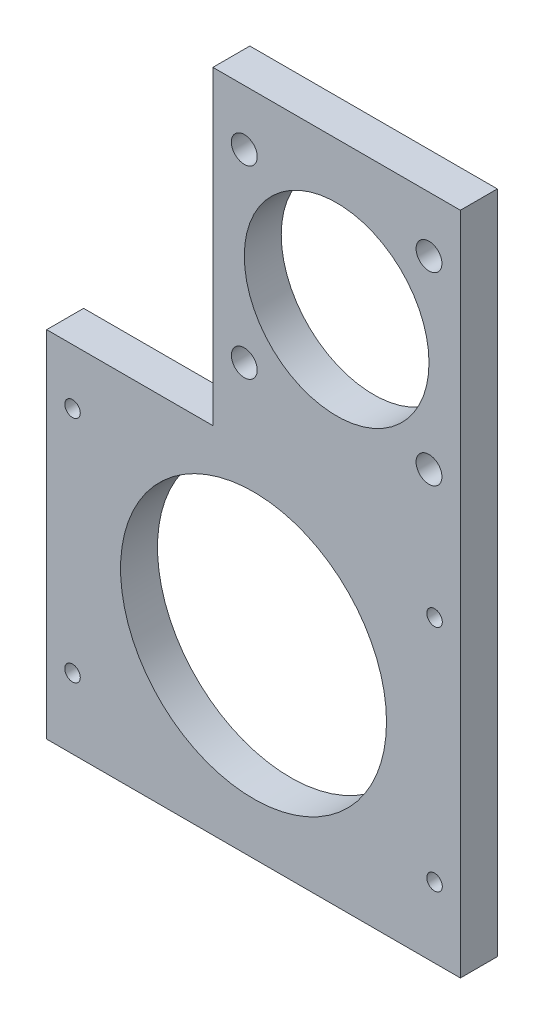
SolidWorks part; units mm, degrees
ref_plane "前视基准面" through (0, 0, 0) normal (0, 0, 1) x (1, 0, 0)
ref_plane "上视基准面" through (0, 0, 0) normal (0, 1, 0) x (1, 0, 0)
ref_plane "右视基准面" through (0, 0, 0) normal (1, 0, 0) x (0, 0, -1)
sketch "草图1" plane through (0, 0, 0) normal (0, 0, 1) x (1, 0, 0)
  line L0 (0, 0) -> (0, 23.9514) construction
  line L1 (-11, 90) -> (56, 90)
  line L2 (-56, 6) -> (-56, -90)
  line L3 (-56, -90) -> (56, -90)
  line L4 (56, 90) -> (56, -90)
  line L5 (-20.7857, 33.4056) -> (56, -90) construction
  line L6 (-56, -90) -> (56, 90) construction
  line L7 (-133.554, 0) -> (85.9905, 0) construction
  line L8 (-11, 90) -> (-11, 6)
  line L9 (-11, 6) -> (-56, 6)
  circle A0 centre (0, -40) radius 36
  circle A1 centre (22.5, 50) radius 25
  point P0 (0, 0)
  dimension "D3" = 96
  dimension "D9" = 50
  dimension "D10" = 72
  dimension "D1" = 112
  dimension "D2" = 180
  dimension "D4" = 67
  dimension "D5" = 40
  dimension "D6" = 50
  dimension "D7" = 56
  dimension "D8" = 33.5
extrude "凸台-拉伸1" add sketch "草图1" along normal blind 10
sketch "草图2" plane through (0, 0, 0) normal (0, 0, -1) x (-1, 0, 0)
  line L1 (-49, -9) -> (49, -9)
  line L2 (-49, -9) -> (-49, -71)
  line L3 (-49, -71) -> (49, -71)
  line L4 (49, -9) -> (49, -71)
  line L5 (-49, -9) -> (49, -71) construction
  line L6 (-49, -71) -> (49, -9) construction
  point P0 (0, -40)
  dimension "D1" = 98
  dimension "D2" = 62
sketch "草图3" plane through (0, 0, 0) normal (0, 0, -1) x (-1, 0, 0)
  line L1 (-47.5, 75) -> (2.5, 75)
  line L2 (-47.5, 75) -> (-47.5, 25)
  line L3 (-47.5, 25) -> (2.5, 25)
  line L4 (2.5, 75) -> (2.5, 25)
  line L5 (-47.5, 75) -> (2.5, 25) construction
  line L6 (-47.5, 25) -> (2.5, 75) construction
  point P0 (-22.5, 50)
  dimension "D1" = 50
hole_wizard "M5 螺纹孔1" positions "3D草图1" profile "草图4" tap size "M5" standard "GB"
sketch3d "3D草图1"
  point P0 (49, -9, 0)
  point P3 (-49, -9, 0)
  point P6 (-49, -71, 0)
  point P9 (49, -71, 0)
sketch "草图4" plane through (49, -9, 0) normal (1, 0, 0) x (0, 1, 0)
  line L0 (0, 0) -> (0, 13.6618)
  line L1 (0, 13.6618) -> (2.1, 12.4)
  line L2 (2.1, 12.4) -> (2.1, 0)
  line L5 (2.1, 0) -> (0, 0)
  line L10 (0, 13.6618) -> (-2.1, 12.4) construction
  line L11 (0, -6.35) -> (0, 107.95) construction
  dimension "螺纹孔钻头直径" = 4.2
  dimension "螺纹孔钻头深度" = 12.4
  dimension "导头角度" = 118
cosmetic thread "孔螺蚊线1" parameters "D1"=10, "D2"=5
cosmetic thread "孔螺蚊线2" parameters "D1"=10, "D2"=5
cosmetic thread "孔螺蚊线3" parameters "D1"=10, "D2"=5
cosmetic thread "孔螺蚊线4" parameters "D1"=10, "D2"=5
hole_wizard "大小mm 暗销槽口1" positions "3D草图2" profile "草图5" size "Ø6.0" standard "GB" slot yes
sketch3d "3D草图2"
  point P0 (47.5, 25, 0)
  point P3 (47.5, 75, 0)
  point P6 (-2.5, 75, 0)
  point P9 (-2.5, 25, 0)
sketch "草图5" plane through (47.5, 25, 0) normal (1, 0, 0) x (0, 1, 0)
  line L0 (0, 0) -> (0, 14.503)
  line L1 (0, 14.503) -> (3.5, 12.4)
  line L2 (3.5, 12.4) -> (3.5, 0)
  line L5 (3.5, 0) -> (0, 0)
  line L10 (0, 14.503) -> (-3.5, 12.4) construction
  line L11 (0, -6.35) -> (0, 107.95) construction
  dimension "孔直径" = 7
  dimension "孔深度" = 12.4
  dimension "导头角度" = 118
